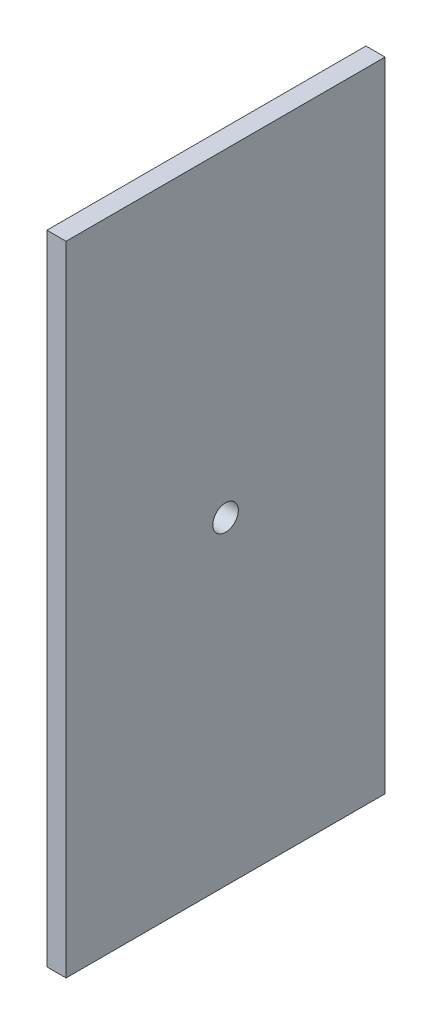
SolidWorks part; units mm, degrees
material "PMMA"
ref_plane "Plan de face" through (0, 0, 0) normal (0, 0, 1) x (1, 0, 0)
ref_plane "Plan de dessus" through (0, 0, 0) normal (0, 1, 0) x (1, 0, 0)
ref_plane "Plan de droite" through (0, 0, 0) normal (1, 0, 0) x (0, 0, -1)
sketch "Esquisse2" plane through (0, 0, 0) normal (0, 0, 1) x (1, 0, 0)
  line L1 (0, 160) -> (6, 160)
  line L2 (0, 160) -> (0, -40)
  line L3 (0, -40) -> (6, -40)
  line L4 (6, 160) -> (6, -40)
  dimension "D1" = 200
  dimension "D2" = 6
extrude "Boss.-Extru.1" add sketch "Esquisse2" along normal blind 100
sketch "Esquisse3" plane through (0, 0, 0) normal (1, 0, 0) x (0, 0, -1)
  line L0 (-100, -40) -> (-100, 160) construction
  line L1 (-100, 160) -> (0, 160) construction
  circle A0 centre (-50, 60) radius 4
  dimension "D1" = 8
  dimension "D2" = 50
  dimension "D3" = 100
extrude "Enlèv. mat.-Extru.1" cut sketch "Esquisse3" along normal through all
